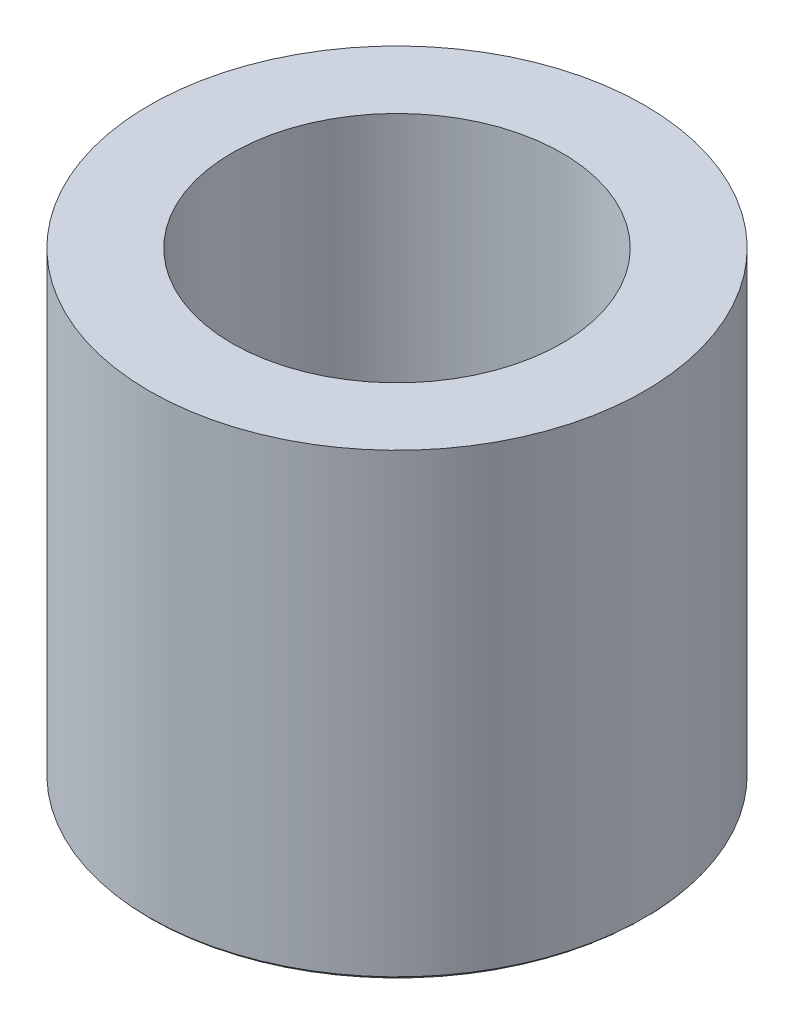
SolidWorks part; units mm, degrees
ref_plane "Front Plane" through (0, 0, 0) normal (0, 0, 1) x (1, 0, 0)
ref_plane "Top Plane" through (0, 0, 0) normal (0, 1, 0) x (1, 0, 0)
ref_plane "Right Plane" through (0, 0, 0) normal (1, 0, 0) x (0, 0, -1)
sketch "Sketch2" plane through (0, 0, 0) normal (0, 0, 1) x (1, 0, 0)
  line L0 (9.58, 0) -> (14.58, 0)
  line L1 (14.58, 0) -> (14.58, -10.8826)
  line L3 (14.08, -11.7487) -> (11.08, -13.4807)
  line L5 (9.58, -12.6147) -> (9.58, 0)
  line L6 (0, 0) -> (0, -6.3381) construction
  arc A0 (9.58, -12.6147) -> (11.08, -13.4807) centre (10.58, -12.6147) ccw
  arc A1 (14.58, -10.8826) -> (14.08, -11.7487) centre (13.58, -10.8826) cw
  point P8 (9.58, -14.3468)
  point P11 (14.58, -11.46)
  dimension "D4" = 1
  dimension "D5" = 1
  dimension "D1" = 14.58
  dimension "D2" = 11.46
  dimension "D3" = 14.3468
revolve "Revolve1" add sketch "Sketch2" angle 360 about L6
sketch "Sketch4" plane through (0, 0, 0) normal (0, 1, 0) x (1, 0, 0)
  circle A0 centre (0, 0) radius 9.58
  circle A1 centre (0, 0) radius 14.58
extrude "Boss-Extrude1" add sketch "Sketch4" along normal blind 15
sketch "Sketch5" plane through (0, 15, 0) normal (0, 1, 0) x (1, 0, 0)
  circle A2 centre (0, 0) radius 14.58
  circle A3 centre (0, 0) radius 14.38
  circle A4 centre (0, 0) radius 14.38
  dimension "D1" = 0.2
extrude "Cut-Extrude1" cut sketch "Sketch5" against normal blind 31
